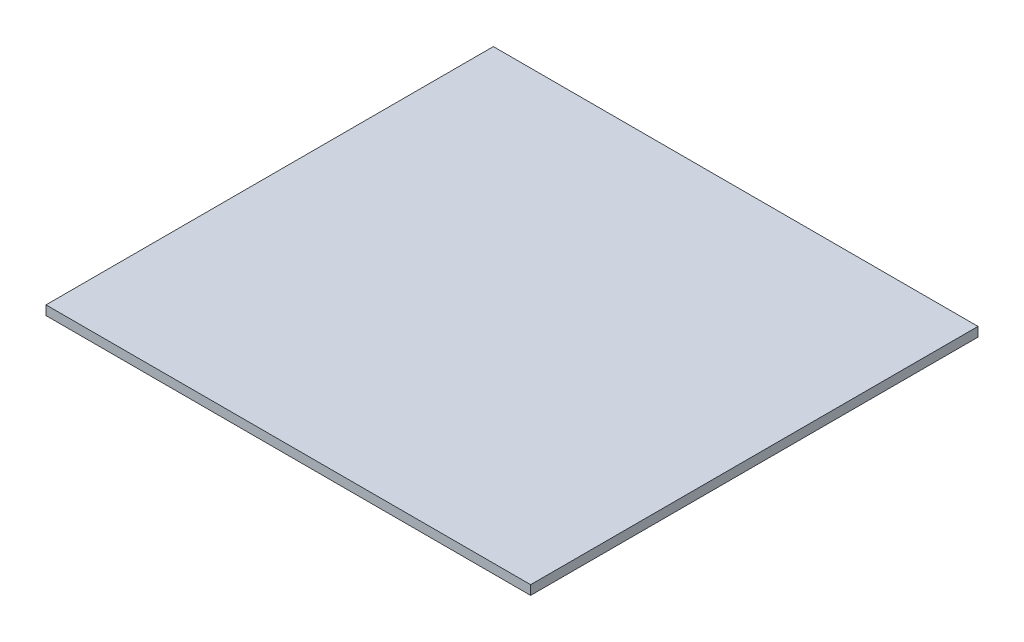
SolidWorks part; units mm, degrees
material "Cedar"
ref_plane "Front Plane" through (0, 0, 0) normal (0, 0, 1) x (1, 0, 0)
ref_plane "Top Plane" through (0, 0, 0) normal (0, 1, 0) x (1, 0, 0)
ref_plane "Right Plane" through (0, 0, 0) normal (1, 0, 0) x (0, 0, -1)
sketch "Sketch1" plane through (0, 0, 0) normal (0, 1, 0) x (1, 0, 0)
  line L1 (0, 0) -> (660.4, 0)
  line L2 (0, 0) -> (0, 609.6)
  line L3 (0, 609.6) -> (660.4, 609.6)
  line L4 (660.4, 0) -> (660.4, 609.6)
  dimension "D1" = 660.4
  dimension "D2" = 609.6
extrude "Boss-Extrude1" add sketch "Sketch1" along normal blind 12.7
sketch "Sketch5" plane through (0, 12.7, 0) normal (0, 1, 0) x (1, 0, 0)
  line L0 (330.2, 609.6) -> (330.2, 464.8281) construction
  line L1 (660.4, 609.6) -> (0, 609.6) construction
  line L2 (0, 0) -> (105.2, 75.1166) construction
  line L3 (660.4, 0) -> (555.2, 75.1166) construction
  line L5 (330.2, 464.8281) -> (105.2, 75.1166) construction
  line L6 (105.2, 75.1166) -> (555.2, 75.1166) construction
  line L7 (555.2, 75.1166) -> (330.2, 464.8281) construction
  line L8 (330.2, 464.8281) -> (330.2, 75.1166) construction
  circle A0 centre (105.2, 75.1166) radius 19.05
  circle A1 centre (555.2, 75.1166) radius 19.05
  circle A2 centre (330.2, 464.8281) radius 19.05
  dimension "D6" = 38.1
  dimension "D7" = 38.1
  dimension "D8" = 38.1
  dimension "D1" = 450
extrude "Cut-Extrude2" [suppressed] cut sketch "Sketch5" against normal through all
sketch "Sketch6" plane through (0, 12.7, 0) normal (0, 1, 0) x (1, 0, 0)
  line L0 (0, 609.6) -> (660.4, 0) construction
  line L1 (660.4, 609.6) -> (0, 0) construction
  point P8 (330.2, 304.8)
sketch "Sketch7" plane through (0, 12.7, 0) normal (0, 1, 0) x (1, 0, 0)
  circle A0 centre (17.9605, 17.9605) radius 17
